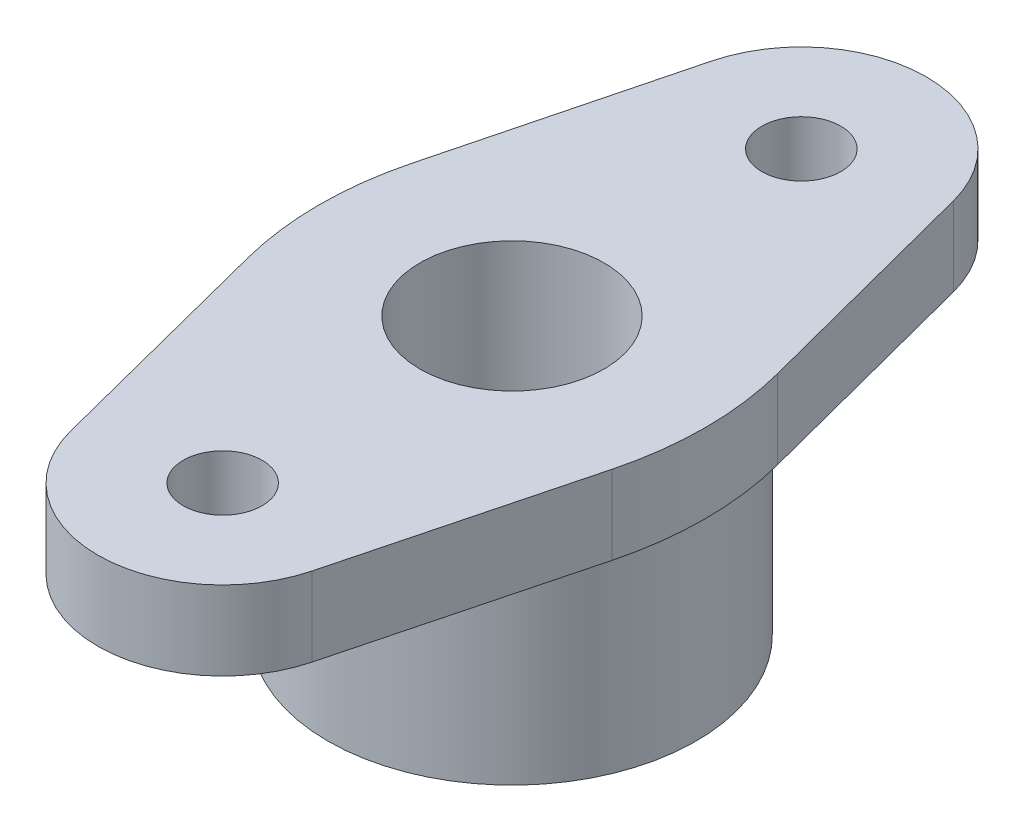
SolidWorks part; units mm, degrees
ref_plane "Front Plane" through (0, 0, 0) normal (0, 0, 1) x (1, 0, 0)
ref_plane "Top Plane" through (0, 0, 0) normal (0, 1, 0) x (1, 0, 0)
ref_plane "Right Plane" through (0, 0, 0) normal (1, 0, 0) x (0, 0, -1)
sketch "Sketch1" plane through (0, 0, 0) normal (0, 1, 0) x (1, 0, 0)
  line L0 (0, 20.8323) -> (0, -24.0012) construction
  line L1 (-37.9676, 0) -> (43.2491, 0) construction
  line L2 (18.3892, 48.7788) -> (31.0654, 0)
  line L3 (-18.4012, 48.7326) -> (-30.9346, 0)
  line L4 (-18.4012, -48.7326) -> (-30.9346, 0)
  line L5 (18.3892, -48.7788) -> (31.0654, 0)
  circle A0 centre (0, 44) radius 19
  circle A1 centre (0, 44) radius 6
  circle A2 centre (0, -44) radius 6
  circle A3 centre (0, -44) radius 19
  circle A4 centre (0, 0) radius 14
  dimension "D1" = 12
  dimension "D2" = 38
  dimension "D5" = 28
  dimension "D3" = 88
  dimension "D4" = 62
extrude "Boss-Extrude1" add sketch "Sketch1" along normal blind 12 contours L4 A3 L5 L2 A0 L3 A4 | A3 A2 | A0 A1
fillet "Fillet1" radius 50 2 edges at (-30.9346, 6, 0) (31.0654, 6, 0)
sketch "Sketch3" plane through (0, 0, 0) normal (0, 0, 1) x (1, 0, 0)
  line L0 (0, 0) -> (0, -17.8068) construction
  line L1 (14, 0) -> (28, 0)
  line L2 (28, 0) -> (28, -30)
  line L3 (28, -30) -> (14, -21.9171)
  line L4 (14, -21.9171) -> (14, 0)
  point P5 (0, 0)
  point P10 (0, 0)
  dimension "D1" = 30
  dimension "D2" = 28
  dimension "D3" = 60
revolve "Revolve1" add sketch "Sketch3" angle 360 about L0
